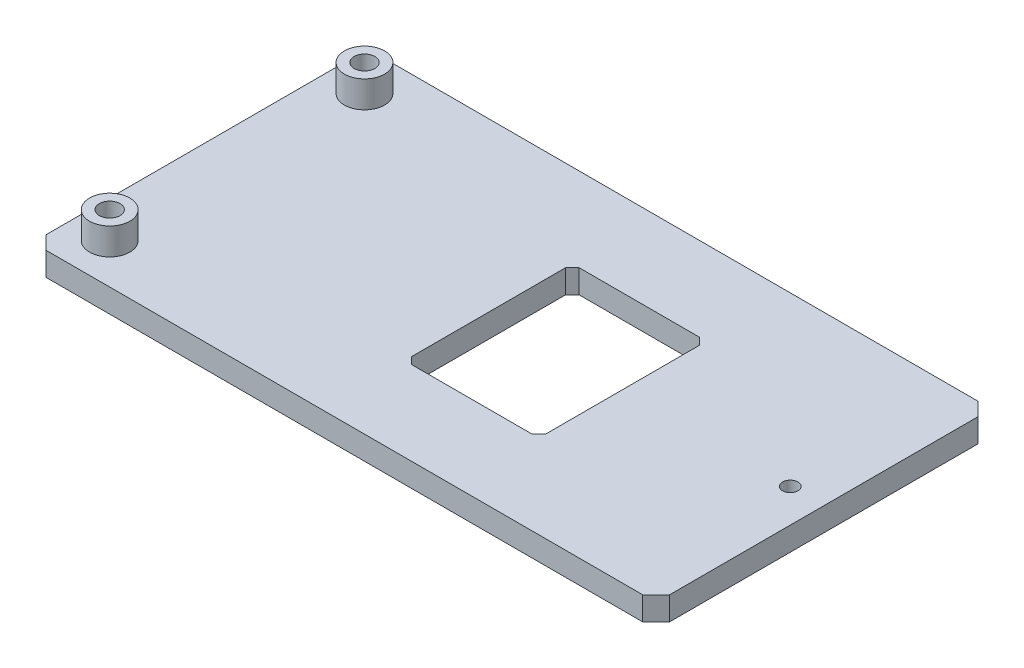
SolidWorks part; units mm, degrees
ref_plane "Front Plane" through (0, 0, 0) normal (0, 0, 1) x (1, 0, 0)
ref_plane "Top Plane" through (0, 0, 0) normal (0, 1, 0) x (1, 0, 0)
ref_plane "Right Plane" through (0, 0, 0) normal (1, 0, 0) x (0, 0, -1)
sketch "Sketch1" plane through (0, 0, 0) normal (0, 1, 0) x (1, 0, 0)
  line L0 (-81.7959, 0) -> (62.292, 0) construction
  line L1 (-48.6743, -25) -> (40.3257, -25)
  line L3 (-48.6743, 25) -> (40.3257, 25)
  line L4 (42.3257, -23) -> (42.3257, 23)
  line L14 (42.3257, 23) -> (40.3257, 25)
  line L15 (-6.6743, -12.5) -> (11.3257, -12.5)
  line L16 (-7.6743, -11.5) -> (-7.6743, 11.5)
  line L17 (-6.6743, 12.5) -> (11.3257, 12.5)
  line L18 (12.3257, -11.5) -> (12.3257, 11.5)
  line L19 (40.3257, -25) -> (42.3257, -23)
  line L20 (12.3257, 11.5) -> (11.3257, 12.5)
  line L21 (-7.6743, 11.5) -> (-6.6743, 12.5)
  line L22 (-6.6743, -12.5) -> (-7.6743, -11.5)
  line L23 (11.3257, -12.5) -> (12.3257, -11.5)
  line L24 (-50.6743, 23) -> (-50.6743, -23)
  line L25 (-48.6743, 25) -> (-50.6743, 23)
  line L26 (-50.6743, -23) -> (-48.6743, -25)
  circle A0 centre (37.3257, 0) radius 1.15
  circle A1 centre (-45.1743, 19) radius 1.55
  circle A2 centre (-45.1743, -19) radius 1.55
  point P0 (-50.6743, -25)
  point P1 (42.3257, 25)
  point P2 (-50.6743, 25)
  point P3 (42.3257, -25)
  point P18 (-7.6743, -12.5)
  point P19 (12.3257, 12.5)
  point P20 (-7.6743, 12.5)
  point P21 (12.3257, -12.5)
  dimension "D6" = 2.3
  dimension "D3" = 3.1
  dimension "D1" = 50
  dimension "D2" = 93
  dimension "D4" = 38
  dimension "D5" = 5.5
  dimension "D8" = 30
  dimension "D9" = 25
  dimension "D10" = 20
extrude "Boss-Extrude1" add sketch "Sketch1" along normal blind 3 and the other way blind 0.5066
sketch "Sketch2" plane through (0, 3, 0) normal (0, 1, 0) x (1, 0, 0)
  line L0 (0, 0) -> (-65.5735, 0) construction
  circle A0 centre (-45.1743, 19) radius 3
  circle A1 centre (-45.1743, -19) radius 3
  circle A2 centre (-45.1743, 19) radius 1.55
  circle A3 centre (-45.1743, 19) radius 1.55 construction
  circle A4 centre (-45.1743, -19) radius 1.55
  dimension "D1" = 6
extrude "Boss-Extrude2" add sketch "Sketch2" along normal blind 4
